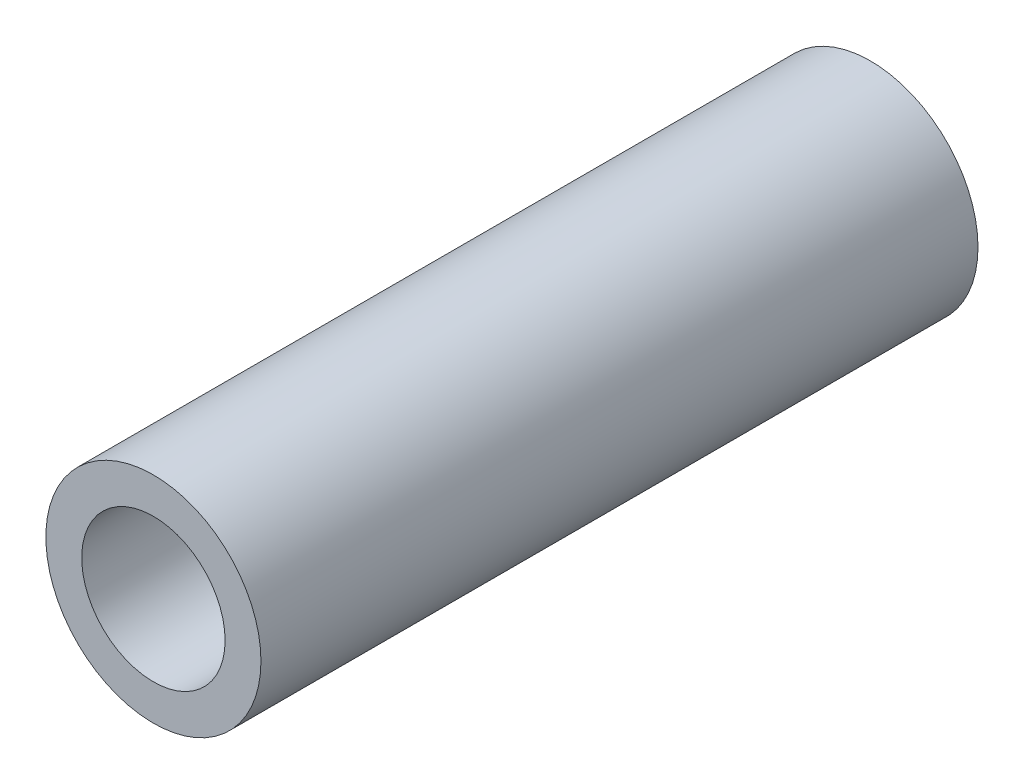
SolidWorks part; units mm, degrees
ref_plane "Front Plane" through (0, 0, 0) normal (0, 0, 1) x (1, 0, 0)
ref_plane "Top Plane" through (0, 0, 0) normal (0, 1, 0) x (1, 0, 0)
ref_plane "Right Plane" through (0, 0, 0) normal (1, 0, 0) x (0, 0, -1)
sketch "Sketch1" plane through (0, 0, 0) normal (0, 0, 1) x (1, 0, 0)
  circle A0 centre (0, 0) radius 3
  circle A1 centre (0, 0) radius 2
extrude "Boss-Extrude1" add sketch "Sketch1" along normal blind 20
